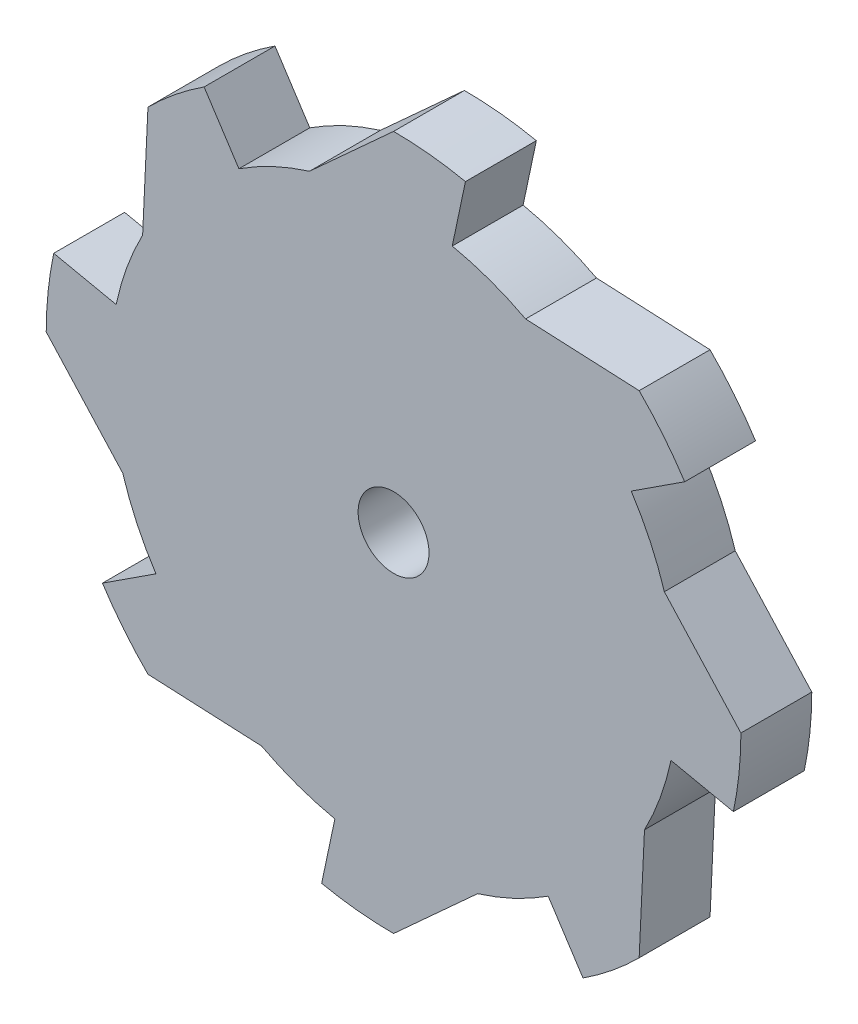
SolidWorks part; units mm, degrees
ref_plane "Front Plane" through (0, 0, 0) normal (0, 0, 1) x (1, 0, 0)
ref_plane "Top Plane" through (0, 0, 0) normal (0, 1, 0) x (1, 0, 0)
ref_plane "Right Plane" through (0, 0, 0) normal (1, 0, 0) x (0, 0, -1)
sketch "Sketch1" plane through (0, 0, 0) normal (0, 0, 1) x (1, 0, 0)
  line L0 (0, 0) -> (60.3776, 0) construction
  line L1 (0, 0) -> (75.1754, 27.3616) construction
  line L3 (95.878, -20.2834) -> (78.2677, -16.5579)
  line L4 (0, 0) -> (70.7981, -37.2509)
  line L6 (0, 0) -> (76.4022, 23.7214) construction
  line L7 (76.4022, 23.7214) -> (98, 0)
  line L8 (0, 0) -> (76.4022, 23.7214)
  arc A0 (70.7981, -37.2509) -> (78.2677, -16.5579) centre (0, 0) ccw
  arc A1 (98, 0) -> (95.878, -20.2834) centre (0, 0) cw
  arc A2 (80, 0) -> (79.978, 1.8761) centre (0, 0) ccw
  arc A3 (80, 0) -> (79.978, 1.8761) centre (0, 0) ccw
  dimension "D1" = 20
  dimension "D3" = 45
  dimension "D2" = 22
extrude "Boss-Extrude1" add sketch "Sketch1" along normal blind 20
pattern_circular "CirPattern1" count 8 every 45 about axis through (0, 0, 0) along (0, 0, 1) of "Boss-Extrude1"
sketch "Sketch2" plane through (0, 0, 0) normal (-0.207, -0.9783, 0) x (0.9783, -0.207, 0)
  line L0 (0, 0) -> (0, 67.6623) construction
  point P3 (0, 67.6623)
sketch "Sketch3" plane through (0, 0, 0) normal (0, 0, 1) x (1, 0, 0)
  circle A0 centre (0, 0) radius 10
extrude "Cut-Extrude1" cut sketch "Sketch3" against normal blind 7 and the other way up to vertex (20 mm away)
